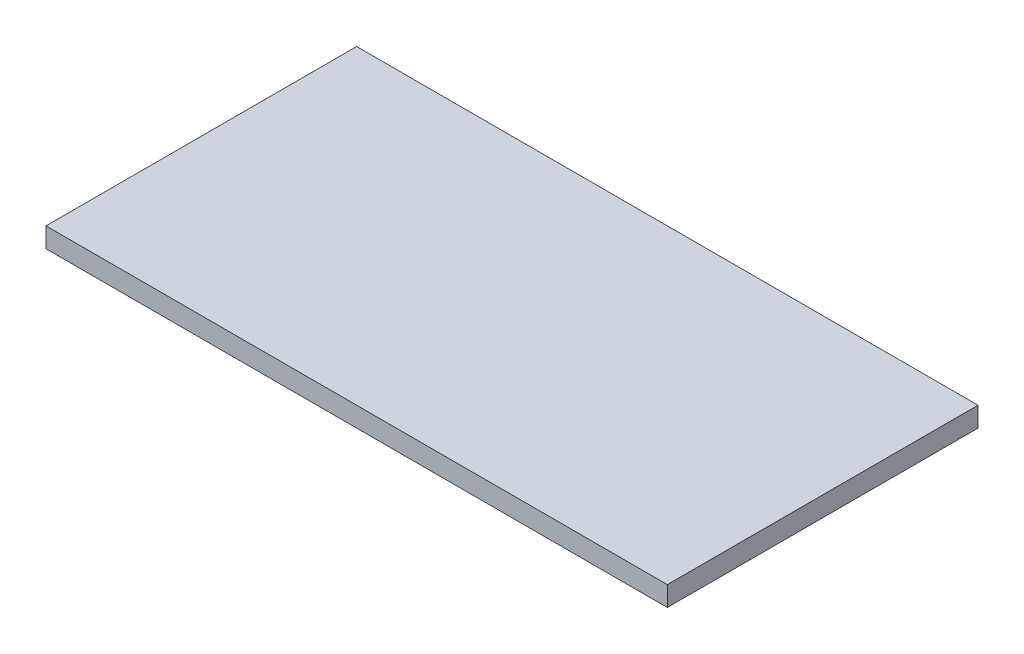
SolidWorks part; units mm, degrees
ref_plane "Спереди" through (0, 0, 0) normal (0, 0, 1) x (1, 0, 0)
ref_plane "Сверху" through (0, 0, 0) normal (0, 1, 0) x (1, 0, 0)
ref_plane "Справа" through (0, 0, 0) normal (1, 0, 0) x (0, 0, -1)
sketch "Эскиз1" plane through (0, 0, 0) normal (0, 1, 0) x (1, 0, 0)
  line L1 (282, -141) -> (-282, -141)
  line L2 (282, -141) -> (282, 141)
  line L3 (282, 141) -> (-282, 141)
  line L4 (-282, -141) -> (-282, 141)
  line L5 (282, -141) -> (-282, 141) construction
  line L6 (282, 141) -> (-282, -141) construction
  point P0 (0, 0)
  dimension "D1" = 282
  dimension "D2" = 564
extrude "Бобышка-Вытянуть1" add sketch "Эскиз1" along normal blind 18
